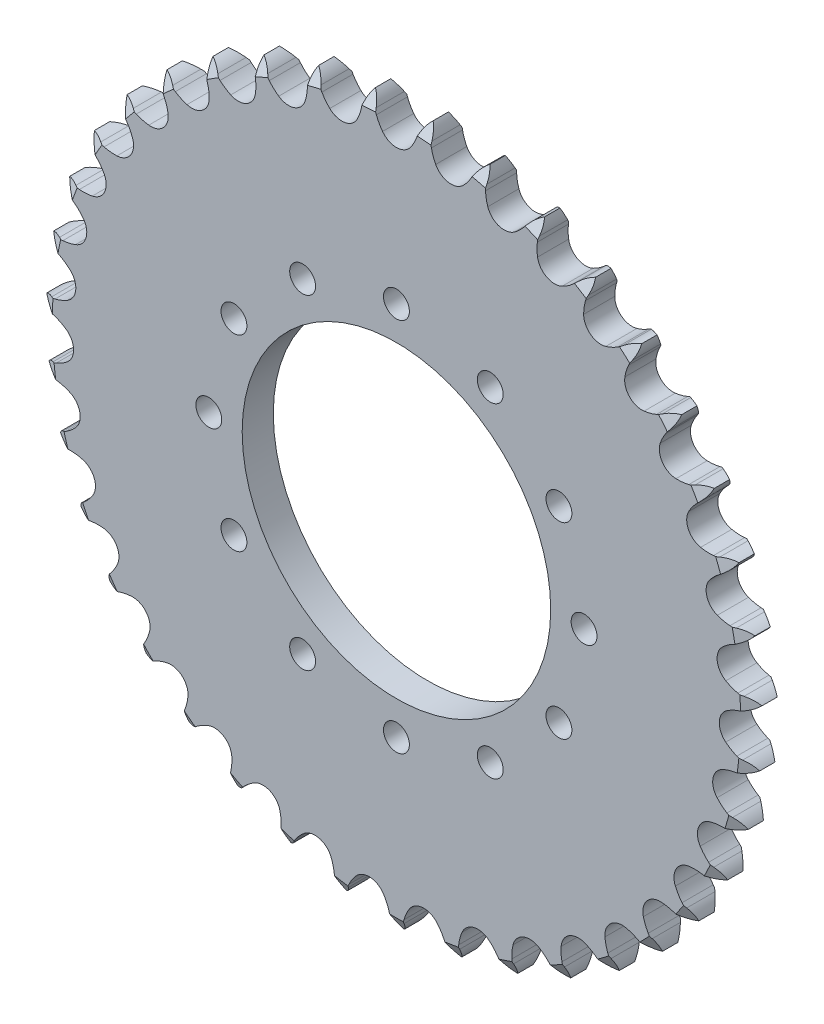
SolidWorks part; units mm, degrees
material "7075-T6 (SN)"
ref_plane "Front Plane" through (0, 0, 0) normal (0, 0, 1) x (1, 0, 0)
ref_plane "Top Plane" through (0, 0, 0) normal (0, 1, 0) x (1, 0, 0)
ref_plane "Right Plane" through (0, 0, 0) normal (1, 0, 0) x (0, 0, -1)
sketch "Work Sketch" plane through (0, 0, 0) normal (0, 0, 1) x (1, 0, 0)
  line L0 (0, 0) -> (0, 160.4542) construction
  line L1 (-112.0919, 78.9148) -> (87.2579, 78.9148) construction
  line L2 (5.102, 120.8822) -> (5.102, 112.9699) construction
  line L3 (-12.8497, 82.6953) -> (16.7256, 82.6953) construction
  line L4 (5.102, 82.6953) -> (-6.0879, 74.4036) construction
  line L5 (5.102, 82.6953) -> (-4.6505, 79.1506) construction
  line L6 (-4.6505, 79.1506) -> (-6.8863, 85.3019)
  line L7 (-11.5114, 78.0206) -> (-7.1525, 78.0206) construction
  line L8 (-11.0765, 124.7602) -> (-11.0765, 110.2345) construction
  line L9 (0, 0) -> (-3.4402, 42.6146) construction
  circle A0 centre (0, 0) radius 78.9148
  circle A1 centre (0, 78.9148) radius 4.0088
  arc A2 (-4.6505, 79.1506) -> (-3.2209, 76.5281) centre (5.0804, 82.7541) ccw
  circle A3 centre (-11.0765, 78.0206) radius 6.4254
  point P23 (-3.2209, 76.5281)
  dimension "D1" = 157.8295
  dimension "D8" = 10.3767
  dimension "D2" = 8.0177
  dimension "D3" = 5.102
  dimension "D4" = 3.7806
  dimension "D5" = 36.538
  dimension "D6" = 16.564
  dimension "D7" = 10.3767
  dimension "D9" = 0.8942
  dimension "D10" = 11.0765
  dimension "D11" = 4.615
sketch "Teeth Sketch" plane through (0, 0, 0) normal (0, 0, 1) x (1, 0, 0)
  line L0 (5.0376, 80.2155) -> (4.6505, 79.1506)
  line L1 (-7.4865, 92.7372) -> (-4.7839, 59.2593) construction
  line L2 (0, 0) -> (-10.9133, 132.3061) construction
  line L3 (7.8951, 79.9848) -> (8.1063, 78.8717)
  line L4 (16093.3137, -199351.4616) -> (-16096.7539, 199394.0762) construction
  line L5 (0, 146.3285) -> (0, 56.9858) construction
  line L6 (17.8398, 78.3686) -> (17.287, 77.3797)
  line L7 (0, -200000) -> (0, 200160.4542) construction
  line L8 (20.6234, 77.6826) -> (20.6533, 76.5499)
  line L9 (-4.6505, 79.1506) -> (-6.8863, 85.3019) construction
  line L10 (44.1616, 67.154) -> (43.8313, 66.0702)
  line L11 (-5.0376, 80.2155) -> (-4.6505, 79.1506)
  line L12 (30.18, 74.4921) -> (29.4757, 73.6046)
  line L13 (32.8175, 73.3684) -> (32.6653, 72.2456)
  line L14 (41.7385, 68.6862) -> (40.901, 67.9232)
  line L15 (52.2161, 61.1014) -> (51.267, 60.4826)
  line L16 (54.362, 59.2003) -> (53.8621, 58.1836)
  line L17 (61.3413, 51.9341) -> (60.3052, 51.4756)
  line L18 (63.1544, 49.7134) -> (62.4979, 48.79)
  line L19 (68.8777, 41.4218) -> (67.7815, 41.1354)
  line L20 (70.3112, 38.939) -> (69.515, 38.1328)
  line L21 (74.6303, 29.8366) -> (73.5023, 29.7298)
  line L22 (75.6469, 27.156) -> (74.7318, 26.488)
  line L23 (78.45, 17.4787) -> (77.3195, 17.5542)
  line L24 (79.0234, 14.6698) -> (78.013, 14.1572)
  line L25 (80.2378, 4.6681) -> (79.1341, 4.9239)
  line L26 (80.3533, 1.8035) -> (79.2737, 1.4597)
  line L27 (79.9476, -8.2634) -> (78.8992, -7.8338)
  line L28 (79.602, -11.1094) -> (78.4813, -11.2756)
  line L29 (77.5867, -20.9809) -> (76.6208, -20.3887)
  line L30 (76.7891, -23.7346) -> (75.6562, -23.7189)
  line L31 (73.2164, -33.155) -> (72.358, -32.4155)
  line L32 (71.9874, -35.7451) -> (70.8717, -35.5478)
  line L33 (66.9499, -44.4704) -> (66.2212, -43.6028)
  line L34 (65.3213, -46.8298) -> (64.2517, -46.4561)
  line L35 (58.9493, -54.634) -> (58.3693, -53.6608)
  line L36 (56.9634, -56.7016) -> (55.9676, -56.1612)
  line L37 (49.422, -63.3827) -> (49.0056, -62.329)
  line L38 (47.1301, -65.1049) -> (46.2339, -64.4118)
  line L39 (38.6147, -70.4897) -> (38.3727, -69.3829)
  line L40 (36.0763, -71.822) -> (35.3028, -70.9941)
  line L41 (26.8073, -75.7712) -> (26.746, -74.6398)
  line L42 (24.088, -76.679) -> (23.4574, -75.7377)
  line L43 (14.3056, -79.0901) -> (14.4266, -77.9636)
  line L44 (11.4759, -79.55) -> (11.0044, -78.5198)
  line L45 (1.4334, -80.3607) -> (1.7335, -79.2682)
  line L46 (-1.4334, -80.3607) -> (-1.7335, -79.2682)
  line L47 (-11.4759, -79.55) -> (-11.0044, -78.5198)
  line L48 (-14.3056, -79.0901) -> (-14.4266, -77.9636)
  line L49 (-24.088, -76.679) -> (-23.4574, -75.7377)
  line L50 (-26.8073, -75.7712) -> (-26.746, -74.6398)
  line L51 (-36.0763, -71.822) -> (-35.3028, -70.9941)
  line L52 (-38.6147, -70.4897) -> (-38.3727, -69.3829)
  line L53 (-47.1301, -65.1049) -> (-46.2339, -64.4118)
  line L54 (-49.422, -63.3827) -> (-49.0056, -62.329)
  line L55 (-56.9634, -56.7016) -> (-55.9676, -56.1612)
  line L56 (-58.9493, -54.634) -> (-58.3693, -53.6608)
  line L57 (-65.3213, -46.8298) -> (-64.2517, -46.4561)
  line L58 (-66.9499, -44.4704) -> (-66.2212, -43.6028)
  line L59 (-71.9874, -35.7451) -> (-70.8717, -35.5478)
  line L60 (-73.2164, -33.155) -> (-72.358, -32.4155)
  line L61 (-76.7891, -23.7346) -> (-75.6562, -23.7189)
  line L62 (-77.5867, -20.9809) -> (-76.6208, -20.3887)
  line L63 (-79.602, -11.1094) -> (-78.4813, -11.2756)
  line L64 (-79.9476, -8.2634) -> (-78.8992, -7.8338)
  line L65 (-80.3533, 1.8035) -> (-79.2737, 1.4597)
  line L66 (-80.2378, 4.6681) -> (-79.1341, 4.9239)
  line L67 (-79.0234, 14.6698) -> (-78.013, 14.1572)
  line L68 (-78.45, 17.4787) -> (-77.3195, 17.5542)
  line L69 (-75.6469, 27.156) -> (-74.7318, 26.488)
  line L70 (-74.6303, 29.8366) -> (-73.5023, 29.7298)
  line L71 (-70.3112, 38.939) -> (-69.515, 38.1328)
  line L72 (-68.8777, 41.4218) -> (-67.7815, 41.1354)
  line L73 (-63.1544, 49.7134) -> (-62.4979, 48.79)
  line L74 (-61.3413, 51.9341) -> (-60.3052, 51.4756)
  line L75 (-54.362, 59.2003) -> (-53.8621, 58.1836)
  line L76 (-52.2161, 61.1014) -> (-51.267, 60.4826)
  line L77 (-44.1616, 67.154) -> (-43.8313, 66.0702)
  line L78 (-41.7385, 68.6862) -> (-40.901, 67.9232)
  line L79 (-32.8175, 73.3684) -> (-32.6653, 72.2456)
  line L80 (-30.18, 74.4921) -> (-29.4757, 73.6046)
  line L81 (-20.6234, 77.6826) -> (-20.6533, 76.5499)
  line L82 (-17.8398, 78.3686) -> (-17.287, 77.3797)
  line L83 (-7.8951, 79.9848) -> (-8.1063, 78.8717)
  arc A0 (-6.8336, 82.8459) -> (-5.0376, 80.2155) centre (-11.0765, 78.0206) cw
  circle A1 centre (-11.0765, 78.0206) radius 6.4254 construction
  arc A2 (-3.2209, 76.5281) -> (-4.6505, 79.1506) centre (5.0804, 82.7541) cw
  arc A3 (-4.6505, 79.1506) -> (-3.2209, 76.5281) centre (5.0804, 82.7541) ccw construction
  circle A4 centre (0, 78.9148) radius 4.0088 construction
  arc A5 (-3.2209, 76.5281) -> (3.2209, 76.5281) centre (0, 78.9148) ccw
  arc A6 (3.2209, 76.5281) -> (4.6505, 79.1506) centre (-5.0804, 82.7541) ccw
  arc A7 (6.8336, 82.8459) -> (5.0376, 80.2155) centre (11.0765, 78.0206) ccw
  arc A8 (6.5443, 82.8692) -> (7.8951, 79.9848) centre (1.5824, 78.787) cw
  arc A9 (9.0967, 76.0537) -> (8.1063, 78.8717) centre (18.2893, 80.8676) cw
  arc A10 (9.0967, 76.0537) -> (15.4552, 75.0204) centre (12.6588, 77.8928) ccw
  arc A11 (15.4552, 75.0204) -> (17.287, 77.3797) centre (8.2601, 82.4975) ccw
  arc A12 (20.0345, 80.6769) -> (17.8398, 78.3686) centre (23.4484, 75.2334) ccw
  arc A13 (19.7528, 80.7463) -> (20.6234, 77.6826) centre (14.2002, 77.5129) cw
  arc A14 (21.1788, 73.6096) -> (20.6533, 76.5499) centre (31.0245, 76.8865) cw
  arc A15 (21.1788, 73.6096) -> (27.2892, 71.5697) centre (24.9898, 74.8535) ccw
  arc A16 (27.2892, 71.5697) -> (29.4757, 73.6046) centre (21.3867, 80.1041) ccw
  arc A17 (32.7165, 76.4184) -> (30.18, 74.4921) centre (35.2131, 70.4978) ccw
  arc A18 (32.4496, 76.5321) -> (32.8175, 73.3684) centre (26.4502, 74.2313) cw
  arc A19 (32.7124, 69.2591) -> (32.6653, 72.2456) centre (42.9562, 70.9142) cw
  arc A20 (32.7124, 69.2591) -> (38.4163, 66.2654) centre (36.6735, 69.8756) ccw
  arc A21 (38.4163, 66.2654) -> (40.901, 67.9232) centre (33.9593, 75.6361) ccw
  arc A22 (44.5512, 70.1807) -> (41.7385, 68.6862) centre (46.0657, 63.9363) ccw
  arc A23 (44.306, 70.3358) -> (44.1616, 67.154) centre (38.0153, 69.0271) cw
  arc A24 (43.3987, 63.1147) -> (43.8313, 66.0702) centre (53.7754, 63.1052) cw
  arc A25 (43.3987, 63.1147) -> (48.5486, 59.2448) centre (47.4074, 63.0878) ccw
  arc A26 (48.5486, 59.2448) -> (51.267, 60.4826) centre (45.6524, 69.2092) ccw
  arc A27 (55.2321, 62.1253) -> (52.2161, 61.1014) centre (55.7253, 55.7189) ccw
  arc A28 (55.0149, 62.3178) -> (54.362, 59.2003) centre (48.5957, 62.0351) cw
  arc A29 (52.961, 55.3358) -> (53.8621, 58.1836) centre (63.2018, 53.6618) cw
  arc A30 (52.961, 55.3358) -> (57.4234, 50.6899) centre (56.9135, 54.6662) ccw
  arc A31 (57.4234, 50.6899) -> (60.3052, 51.4756) centre (56.1632, 60.9898) ccw
  arc A32 (64.4824, 52.461) -> (61.3413, 51.9341) centre (63.9416, 46.0584) ccw
  arc A33 (64.2989, 52.6858) -> (63.1544, 49.7134) centre (57.9175, 53.4365) cw
  arc A34 (61.1517, 46.1237) -> (62.4979, 48.79) centre (70.9913, 42.8287) cw
  arc A35 (61.1517, 46.1237) -> (64.811, 40.8221) centre (64.9456, 44.8287) ccw
  arc A36 (64.811, 40.8221) -> (67.7815, 41.1354) centre (65.2193, 51.1908) ccw
  arc A37 (72.0627, 41.4379) -> (68.8777, 41.4218) centre (70.5018, 35.205) ccw
  arc A38 (71.9177, 41.6892) -> (70.3112, 38.939) centre (65.7393, 43.4539) cw
  arc A39 (67.7585, 35.717) -> (69.515, 38.1328) centre (76.9422, 30.8862) cw
  arc A40 (67.7585, 35.717) -> (70.5201, 29.8971) centre (71.2956, 33.8302) ccw
  arc A41 (70.5201, 29.8971) -> (73.5023, 29.7298) centre (72.5864, 40.0659) ccw
  arc A42 (77.7767, 29.3416) -> (74.6303, 29.8366) centre (75.2361, 23.4398) ccw
  arc A43 (77.6738, 29.6129) -> (75.6469, 27.156) centre (71.8585, 32.3458) cw
  arc A44 (72.6105, 24.3852) -> (74.7318, 26.488) centre (80.9003, 18.1439) cw
  arc A45 (72.6105, 24.3852) -> (74.4027, 18.1977) centre (75.7991, 21.9555) ccw
  arc A46 (74.4027, 18.1977) -> (77.3195, 17.5542) centre (78.0734, 27.9034) ccw
  arc A47 (81.4762, 16.4854) -> (78.45, 17.4787) centre (78.0218, 11.0675) ccw
  arc A48 (81.4182, 16.7697) -> (79.0234, 14.6698) centre (76.1166, 20.4) cw
  arc A49 (75.5818, 12.4219) -> (78.013, 14.1572) centre (82.7631, 4.9316) cw
  arc A50 (75.5818, 12.4219) -> (76.3583, 6.027) centre (78.3394, 9.5121) ccw
  arc A51 (76.3583, 6.027) -> (79.1341, 4.9239) centre (81.5384, 15.0182) ccw
  arc A52 (83.0656, 3.2022) -> (80.2378, 4.6681) centre (78.7868, -1.5914) ccw
  arc A53 (83.0539, 3.4922) -> (80.3533, 1.8035) centre (78.4033, 7.9259) cw
  arc A54 (76.5957, 0.1368) -> (79.2737, 1.4597) centre (82.4825, -8.4084) cw
  arc A55 (76.5957, 0.1368) -> (76.3363, -6.2998) centre (78.8508, -3.1776) ccw
  arc A56 (76.3363, -6.2998) -> (78.8992, -7.8338) centre (82.8916, 1.7441) ccw
  arc A57 (82.5035, -10.1639) -> (79.9476, -8.2634) centre (77.5113, -14.2091) ccw
  arc A58 (82.5385, -9.8758) -> (79.602, -11.1094) centre (78.6594, -4.7535) cw
  arc A59 (75.6257, -12.1517) -> (78.4813, -11.2756) centre (80.0655, -21.5307) cw
  arc A60 (75.6257, -12.1517) -> (74.3372, -18.4634) centre (77.3199, -15.785) ccw
  arc A61 (74.3372, -18.4634) -> (76.6208, -20.3887) centre (82.0979, -11.5753) ccw
  arc A62 (79.8047, -23.2668) -> (77.5867, -20.9809) centre (74.2283, -26.4587) ccw
  arc A63 (79.8855, -22.9881) -> (76.7891, -23.7346) centre (76.8783, -17.3098) cw
  arc A64 (72.6971, -24.1256) -> (75.6562, -23.7189) centre (75.5749, -34.0953) cw
  arc A65 (72.6971, -24.1256) -> (70.4128, -30.1488) centre (73.7866, -27.9836) ccw
  arc A66 (70.4128, -30.1488) -> (72.358, -32.4155) centre (79.178, -24.5948) ccw
  arc A67 (75.039, -35.7671) -> (73.2164, -33.155) centre (69.0227, -38.0232) ccw
  arc A68 (75.1634, -35.5049) -> (71.9874, -35.7451) centre (73.106, -29.4178) cw
  arc A69 (67.8857, -35.4746) -> (70.8717, -35.5478) centre (69.127, -45.7768) cw
  arc A70 (67.8857, -35.4746) -> (64.6648, -41.0534) centre (68.3422, -39.4574) ccw
  arc A71 (64.6648, -41.0534) -> (66.2212, -43.6028) centre (74.2074, -36.9773) ccw
  arc A72 (68.3299, -47.341) -> (66.9499, -44.4704) centre (62.0296, -48.6028) ccw
  arc A73 (68.4947, -47.1022) -> (65.3213, -46.8298) centre (67.4404, -40.7639) cw
  arc A74 (61.3161, -45.9049) -> (64.2517, -46.4561) centre (60.8887, -56.2728) cw
  arc A75 (61.3161, -45.9049) -> (57.2419, -50.8948) centre (61.1278, -49.9093) ccw
  arc A76 (57.2419, -50.8948) -> (58.3693, -53.6608) centre (67.3148, -48.4022) ccw
  arc A77 (59.851, -57.6888) -> (58.9493, -54.634) centre (53.4299, -57.9236) ccw
  arc A78 (60.052, -57.4796) -> (56.9634, -56.7016) centre (60.0281, -51.0542) cw
  arc A79 (53.1584, -55.1462) -> (55.9676, -56.1612) centre (51.0734, -65.3113) cw
  arc A80 (53.1584, -55.1462) -> (48.3366, -59.4179) centre (52.3302, -59.0685) ccw
  arc A81 (48.3366, -59.4179) -> (49.0056, -62.329) centre (58.6789, -58.5735) ccw
  arc A82 (49.822, -66.5425) -> (49.422, -63.3827) centre (43.4464, -65.7443) ccw
  arc A83 (50.054, -66.3682) -> (47.1301, -65.1049) centre (51.0611, -60.0222) cw
  arc A84 (43.6239, -62.9593) -> (46.2339, -64.4118) centre (39.9354, -72.6583) cw
  arc A85 (43.6239, -62.9593) -> (38.1793, -66.4022) centre (42.1772, -66.698) ccw
  arc A86 (38.1793, -66.4022) -> (38.3727, -69.3829) centre (48.5231, -67.2277) ccw
  arc A87 (38.5026, -73.6728) -> (38.6147, -70.4897) centre (32.3376, -71.8622) ccw
  arc A88 (38.7596, -73.538) -> (36.0763, -71.822) centre (40.7716, -67.4357) cw
  arc A89 (32.9596, -69.1417) -> (35.3028, -70.9941) centre (27.763, -78.1234) cw
  arc A90 (32.9596, -69.1417) -> (27.0333, -71.6667) centre (30.932, -72.6) ccw
  arc A91 (27.0333, -71.6667) -> (26.746, -74.6398) centre (37.1107, -74.1408) ccw
  arc A92 (26.1861, -78.8951) -> (26.8073, -75.7712) centre (20.3913, -76.1189) ccw
  arc A93 (26.4613, -78.8032) -> (24.088, -76.679) centre (29.4261, -73.1027) cw
  arc A94 (21.4417, -73.5335) -> (23.4574, -75.7377) centre (14.8716, -81.5653) cw
  arc A95 (21.4417, -73.5335) -> (15.187, -75.0751) centre (18.8855, -76.6216) ccw
  arc A96 (15.187, -75.0751) -> (14.4266, -77.9636) centre (24.7371, -79.1336) ccw
  arc A97 (13.1913, -82.0739) -> (14.3056, -79.0901) centre (7.9169, -78.4042) ccw
  arc A98 (13.4777, -82.0274) -> (11.4759, -79.55) centre (17.3186, -76.8763) cw
  arc A99 (9.3684, -76.0207) -> (11.0044, -78.5198) centre (1.595, -82.8946) cw
  arc A100 (9.3684, -76.0207) -> (2.9475, -76.5391) centre (6.35, -78.6589) ccw
  arc A101 (2.9475, -76.5391) -> (1.7335, -79.2682) centre (11.7228, -82.077) ccw
  arc A102 (-0.1451, -83.1271) -> (1.4334, -80.3607) centre (-4.7625, -78.6589) ccw
  arc A103 (0.1451, -83.1271) -> (-1.4334, -80.3607) centre (4.7625, -78.6589) cw
  arc A104 (-2.9475, -76.5391) -> (-1.7335, -79.2682) centre (-11.7228, -82.077) cw
  arc A105 (-2.9475, -76.5391) -> (-9.3684, -76.0207) centre (-6.35, -78.6589) ccw
  arc A106 (-9.3684, -76.0207) -> (-11.0044, -78.5198) centre (-1.595, -82.8946) ccw
  arc A107 (-13.4777, -82.0274) -> (-11.4759, -79.55) centre (-17.3186, -76.8763) ccw
  arc A108 (-13.1913, -82.0739) -> (-14.3056, -79.0901) centre (-7.9169, -78.4042) cw
  arc A109 (-15.187, -75.0751) -> (-14.4266, -77.9636) centre (-24.7371, -79.1336) cw
  arc A110 (-15.187, -75.0751) -> (-21.4417, -73.5335) centre (-18.8855, -76.6216) ccw
  arc A111 (-21.4417, -73.5335) -> (-23.4574, -75.7377) centre (-14.8716, -81.5653) ccw
  arc A112 (-26.4613, -78.8032) -> (-24.088, -76.679) centre (-29.4261, -73.1027) ccw
  arc A113 (-26.1861, -78.8951) -> (-26.8073, -75.7712) centre (-20.3913, -76.1189) cw
  arc A114 (-27.0333, -71.6667) -> (-26.746, -74.6398) centre (-37.1107, -74.1408) cw
  arc A115 (-27.0333, -71.6667) -> (-32.9596, -69.1417) centre (-30.932, -72.6) ccw
  arc A116 (-32.9596, -69.1417) -> (-35.3028, -70.9941) centre (-27.763, -78.1234) ccw
  arc A117 (-38.7596, -73.538) -> (-36.0763, -71.822) centre (-40.7716, -67.4357) ccw
  arc A118 (-38.5026, -73.6728) -> (-38.6147, -70.4897) centre (-32.3376, -71.8622) cw
  arc A119 (-38.1793, -66.4022) -> (-38.3727, -69.3829) centre (-48.5231, -67.2277) cw
  arc A120 (-38.1793, -66.4022) -> (-43.6239, -62.9593) centre (-42.1772, -66.698) ccw
  arc A121 (-43.6239, -62.9593) -> (-46.2339, -64.4118) centre (-39.9354, -72.6583) ccw
  arc A122 (-50.054, -66.3682) -> (-47.1301, -65.1049) centre (-51.0611, -60.0222) ccw
  arc A123 (-49.822, -66.5425) -> (-49.422, -63.3827) centre (-43.4464, -65.7443) cw
  arc A124 (-48.3366, -59.4179) -> (-49.0056, -62.329) centre (-58.6789, -58.5735) cw
  arc A125 (-48.3366, -59.4179) -> (-53.1584, -55.1462) centre (-52.3302, -59.0685) ccw
  arc A126 (-53.1584, -55.1462) -> (-55.9676, -56.1612) centre (-51.0734, -65.3113) ccw
  arc A127 (-60.052, -57.4796) -> (-56.9634, -56.7016) centre (-60.0281, -51.0542) ccw
  arc A128 (-59.851, -57.6888) -> (-58.9493, -54.634) centre (-53.4299, -57.9236) cw
  arc A129 (-57.2419, -50.8948) -> (-58.3693, -53.6608) centre (-67.3148, -48.4022) cw
  arc A130 (-57.2419, -50.8948) -> (-61.3161, -45.9049) centre (-61.1278, -49.9093) ccw
  arc A131 (-61.3161, -45.9049) -> (-64.2517, -46.4561) centre (-60.8887, -56.2728) ccw
  arc A132 (-68.4947, -47.1022) -> (-65.3213, -46.8298) centre (-67.4404, -40.7639) ccw
  arc A133 (-68.3299, -47.341) -> (-66.9499, -44.4704) centre (-62.0296, -48.6028) cw
  arc A134 (-64.6648, -41.0534) -> (-66.2212, -43.6028) centre (-74.2074, -36.9773) cw
  arc A135 (-64.6648, -41.0534) -> (-67.8857, -35.4746) centre (-68.3422, -39.4574) ccw
  arc A136 (-67.8857, -35.4746) -> (-70.8717, -35.5478) centre (-69.127, -45.7768) ccw
  arc A137 (-75.1634, -35.5049) -> (-71.9874, -35.7451) centre (-73.106, -29.4178) ccw
  arc A138 (-75.039, -35.7671) -> (-73.2164, -33.155) centre (-69.0227, -38.0232) cw
  arc A139 (-70.4128, -30.1488) -> (-72.358, -32.4155) centre (-79.178, -24.5948) cw
  arc A140 (-70.4128, -30.1488) -> (-72.6971, -24.1256) centre (-73.7866, -27.9836) ccw
  arc A141 (-72.6971, -24.1256) -> (-75.6562, -23.7189) centre (-75.5749, -34.0953) ccw
  arc A142 (-79.8855, -22.9881) -> (-76.7891, -23.7346) centre (-76.8783, -17.3098) ccw
  arc A143 (-79.8047, -23.2668) -> (-77.5867, -20.9809) centre (-74.2283, -26.4587) cw
  arc A144 (-74.3372, -18.4634) -> (-76.6208, -20.3887) centre (-82.0979, -11.5753) cw
  arc A145 (-74.3372, -18.4634) -> (-75.6257, -12.1517) centre (-77.3199, -15.785) ccw
  arc A146 (-75.6257, -12.1517) -> (-78.4813, -11.2756) centre (-80.0655, -21.5307) ccw
  arc A147 (-82.5385, -9.8758) -> (-79.602, -11.1094) centre (-78.6594, -4.7535) ccw
  arc A148 (-82.5035, -10.1639) -> (-79.9476, -8.2634) centre (-77.5113, -14.2091) cw
  arc A149 (-76.3363, -6.2998) -> (-78.8992, -7.8338) centre (-82.8916, 1.7441) cw
  arc A150 (-76.3363, -6.2998) -> (-76.5957, 0.1368) centre (-78.8508, -3.1776) ccw
  arc A151 (-76.5957, 0.1368) -> (-79.2737, 1.4597) centre (-82.4825, -8.4084) ccw
  arc A152 (-83.0539, 3.4922) -> (-80.3533, 1.8035) centre (-78.4033, 7.9259) ccw
  arc A153 (-83.0656, 3.2022) -> (-80.2378, 4.6681) centre (-78.7868, -1.5914) cw
  arc A154 (-76.3583, 6.027) -> (-79.1341, 4.9239) centre (-81.5384, 15.0182) cw
  arc A155 (-76.3583, 6.027) -> (-75.5818, 12.4219) centre (-78.3394, 9.5121) ccw
  arc A156 (-75.5818, 12.4219) -> (-78.013, 14.1572) centre (-82.7631, 4.9316) ccw
  arc A157 (-81.4182, 16.7697) -> (-79.0234, 14.6698) centre (-76.1166, 20.4) ccw
  arc A158 (-81.4762, 16.4854) -> (-78.45, 17.4787) centre (-78.0218, 11.0675) cw
  arc A159 (-74.4027, 18.1977) -> (-77.3195, 17.5542) centre (-78.0734, 27.9034) cw
  arc A160 (-74.4027, 18.1977) -> (-72.6105, 24.3852) centre (-75.7991, 21.9555) ccw
  arc A161 (-72.6105, 24.3852) -> (-74.7318, 26.488) centre (-80.9003, 18.1439) ccw
  arc A162 (-77.6738, 29.6129) -> (-75.6469, 27.156) centre (-71.8585, 32.3458) ccw
  arc A163 (-77.7767, 29.3416) -> (-74.6303, 29.8366) centre (-75.2361, 23.4398) cw
  arc A164 (-70.5201, 29.8971) -> (-73.5023, 29.7298) centre (-72.5864, 40.0659) cw
  arc A165 (-70.5201, 29.8971) -> (-67.7585, 35.717) centre (-71.2956, 33.8302) ccw
  arc A166 (-67.7585, 35.717) -> (-69.515, 38.1328) centre (-76.9422, 30.8862) ccw
  arc A167 (-71.9177, 41.6892) -> (-70.3112, 38.939) centre (-65.7393, 43.4539) ccw
  arc A168 (-72.0627, 41.4379) -> (-68.8777, 41.4218) centre (-70.5018, 35.205) cw
  arc A169 (-64.811, 40.8221) -> (-67.7815, 41.1354) centre (-65.2193, 51.1908) cw
  arc A170 (-64.811, 40.8221) -> (-61.1517, 46.1237) centre (-64.9456, 44.8287) ccw
  arc A171 (-61.1517, 46.1237) -> (-62.4979, 48.79) centre (-70.9913, 42.8287) ccw
  arc A172 (-64.2989, 52.6858) -> (-63.1544, 49.7134) centre (-57.9175, 53.4365) ccw
  arc A173 (-64.4824, 52.461) -> (-61.3413, 51.9341) centre (-63.9416, 46.0584) cw
  arc A174 (-57.4234, 50.6899) -> (-60.3052, 51.4756) centre (-56.1632, 60.9898) cw
  arc A175 (-57.4234, 50.6899) -> (-52.961, 55.3358) centre (-56.9135, 54.6662) ccw
  arc A176 (-52.961, 55.3358) -> (-53.8621, 58.1836) centre (-63.2018, 53.6618) ccw
  arc A177 (-55.0149, 62.3178) -> (-54.362, 59.2003) centre (-48.5957, 62.0351) ccw
  arc A178 (-55.2321, 62.1253) -> (-52.2161, 61.1014) centre (-55.7253, 55.7189) cw
  arc A179 (-48.5486, 59.2448) -> (-51.267, 60.4826) centre (-45.6524, 69.2092) cw
  arc A180 (-48.5486, 59.2448) -> (-43.3987, 63.1147) centre (-47.4074, 63.0878) ccw
  arc A181 (-43.3987, 63.1147) -> (-43.8313, 66.0702) centre (-53.7754, 63.1052) ccw
  arc A182 (-44.306, 70.3358) -> (-44.1616, 67.154) centre (-38.0153, 69.0271) ccw
  arc A183 (-44.5512, 70.1807) -> (-41.7385, 68.6862) centre (-46.0657, 63.9363) cw
  arc A184 (-38.4163, 66.2654) -> (-40.901, 67.9232) centre (-33.9593, 75.6361) cw
  arc A185 (-38.4163, 66.2654) -> (-32.7124, 69.2591) centre (-36.6735, 69.8756) ccw
  arc A186 (-32.7124, 69.2591) -> (-32.6653, 72.2456) centre (-42.9562, 70.9142) ccw
  arc A187 (-32.4496, 76.5321) -> (-32.8175, 73.3684) centre (-26.4502, 74.2313) ccw
  arc A188 (-32.7165, 76.4184) -> (-30.18, 74.4921) centre (-35.2131, 70.4978) cw
  arc A189 (-27.2892, 71.5697) -> (-29.4757, 73.6046) centre (-21.3867, 80.1041) cw
  arc A190 (-27.2892, 71.5697) -> (-21.1788, 73.6096) centre (-24.9898, 74.8535) ccw
  arc A191 (-21.1788, 73.6096) -> (-20.6533, 76.5499) centre (-31.0245, 76.8865) ccw
  arc A192 (-19.7528, 80.7463) -> (-20.6234, 77.6826) centre (-14.2002, 77.5129) ccw
  arc A193 (-20.0345, 80.6769) -> (-17.8398, 78.3686) centre (-23.4484, 75.2334) cw
  arc A194 (-15.4552, 75.0204) -> (-17.287, 77.3797) centre (-8.2601, 82.4975) cw
  arc A195 (-15.4552, 75.0204) -> (-9.0967, 76.0537) centre (-12.6588, 77.8928) ccw
  arc A196 (-9.0967, 76.0537) -> (-8.1063, 78.8717) centre (-18.2893, 80.8676) ccw
  arc A197 (-6.5443, 82.8692) -> (-7.8951, 79.9848) centre (-1.5824, 78.787) ccw
  point P77 (0, 0)
  dimension "D1" = 4.615
  dimension "D2" = 4.715
  dimension "D3" = 39
extrude "Extrusion" add sketch "Teeth Sketch" along normal blind 7.2136
sketch "Sketch1" plane through (0, 0, 0) normal (0, 0, -1) x (-1, 0, 0)
  circle A0 centre (0, 0) radius 78.9443
  circle A1 centre (0, 0) radius 35.7643
  dimension "D1" = 43.18
extrude "Cut-Extrude" cut sketch "Sketch1" against normal through all both and the other way through all contours A1
ref_axis "Axis1" [suppressed] through (0, 0, 7.2136) along (0, 0, -1)
ref_plane "Sprocket Center Plane" through (0, 0, 3.6068) normal (0, 0, 1) x (1, 0, 0)
sketch "Pitch Circle" plane through (0, 0, 3.6068) normal (0, 0, -1) x (-1, 0, 0)
  circle A0 centre (0, 0) radius 82.9531 construction
  dimension "D1" = 165.9063
sketch "Chain Pitch Circle" plane through (0, 0, 0) normal (0, 0, -1) x (-1, 0, 0)
  circle A0 centre (0, 0) radius 82.9531 construction
  dimension "D1" = 165.9063
ref_plane "Center Plane" through (0, 0, 3.6068) normal (0, 0, 1) x (1, 0, 0)
hole_wizard "Ø6.0mm Dowel Hole1" positions "Sketch7" profile "Sketch8" hole size "Ø6.0" standard "ANSI Metric" end condition through all
sketch "Sketch7" plane through (0, 0, 7.2136) normal (0, 0, 1) x (1, 0, 0)
  point P0 (-43.5, 0)
  dimension "D1" = 43.5
sketch "Sketch8" plane through (-43.5, 0, 7.2136) normal (1, 0, 0) x (0, -1, 0)
  line L0 (0, 0) -> (0, 7.2136)
  line L1 (0, 7.2136) -> (3, 7.2136)
  line L2 (3, 7.2136) -> (3, 0)
  line L5 (3, 0) -> (0, 0)
  line L11 (0, -6.35) -> (0, 107.95) construction
  dimension "Thru Hole Dia." = 6
  dimension "Thru Hole Depth" = 7.2136
pattern_circular "CirPattern1" count 12 over 360 about axis through (0, 0, 0) along (0, 0, 1) of "Ø6.0mm Dowel Hole1"
sketch "Sketch5" plane through (0, 0, 0) normal (1, 0, 0) x (0, 0, -1)
  line L0 (-1.8288, -82.9722) -> (-5.3848, -82.9722)
  line L3 (-5.3848, -79.7786) -> (-7.2136, -79.7786)
  line L5 (-7.2136, -79.7786) -> (-7.2136, -82.9722)
  line L6 (-7.2136, -82.9722) -> (-5.3848, -82.9722)
  line L7 (-7.2136, -82.9722) -> (0, -82.9722) construction
  line L8 (-7.2136, -82.9722) -> (0, -82.9722)
  line L9 (-5.3848, -82.9722) -> (-7.2136, -79.7786)
  line L10 (-5.3848, -79.7786) -> (-5.3848, -82.9722)
  point P5 (-3.6068, -82.9722)
  dimension "D1" = 3.556
  dimension "D2" = 3.1936
  dimension "D3" = 1.8288
revolve "Cut-Revolve1" cut sketch "Sketch5" angle 360 about axis through (0, 0, 7.2136) along (0, 0, -1)
mirror "Mirror1" about plane through (0, 0, 3.6068) normal (0, 0, 1) of "Cut-Revolve1"
equation "\"P\"= 0.500'//Chain Pitch"
equation "\"N\"= 39'//Number of Teeth"
equation "\"Dr\"= 5 / 16'//Roller Diameter"
equation "\"Ds\"= 1.0005 * \"Dr\" + 0.003'Seating Curve DIameter"
equation "\"R\"= \"Ds\" / 2"
equation "\"A\"= 35 + 60 / \"N\""
equation "\"B\"= 18 - 56 / \"N\""
equation "\"ac\"= 0.8 * \"Dr\""
equation "\"M\"= 0.8 * \"Dr\" * cos ( 35 + 60 / \"N\" )"
equation "\"T\"= 0.8 * \"Dr\" * sin ( 35 + 60 / \"N\" )"
equation "\"E\"= 1.3025 * \"Dr\" + 0.0015"
equation "\"Chordal Length of Arc xy\"= ( 2.605 * \"Dr\" + 0.003 ) * sin ( 9 - 28 / \"N\" )"
equation "\"yz\"= \"Dr\" * ( 1.4 * sin ( 17 - 64 / \"N\" ) - 0.8 * sin ( 18 - 56 / \"N\" ) )"
equation "\"ab\"= 1.4 * \"Dr\""
equation "\"W\"= 1.4 * \"Dr\" * cos ( 180 / \"N\" )"
equation "\"V\"= 1.4 * \"Dr\" * sin ( 180 / \"N\" )"
equation "\"F\"= \"Dr\" * ( 0.8 * cos ( 18 - 56 / \"N\" ) + 1.4 * cos ( 17 - 64 / \"N\" ) - 1.3025 )"
equation "\"H\"= sqr ( \"F\" ^ 2 - ( 1.4 * \"Dr\" - \"P\" / 2 ) ^ 2 )"
equation "\"S\"= \"P\" / 2 * cos ( 180 / \"N\" ) + \"H\" * sin ( 180 / \"N\" )"
equation "\"PD\"= \"P\" / ( sin ( 180 / \"N\" ) )"
equation "\"D1@Work Sketch\" = \"PD\""
equation "\"D3@Work Sketch\" = \"M\""
equation "\"D4@Work Sketch\" = \"T\""
equation "\"D5@Work Sketch\" = \"A\""
equation "\"D6@Work Sketch\" = \"B\""
equation "\"D7@Work Sketch\" = \"E\""
equation "\"D8@Work Sketch\" = \"E\""
equation "\"D9@Work Sketch\" = \"V\""
equation "\"D10@Work Sketch\" = \"W\""
equation "\"D2@Work Sketch\" = \"R\" * 2"
equation "\"D11@Work Sketch\" = 180 / \"N\""
equation "\"D2@Teeth Sketch\" = 180 / \"N\" + 0.1"
equation "\"D3@Teeth Sketch\" = \"N\""
equation "\"Edge Thickness\"=1.7"
equation "\"D1@Sketch1\"=\"Edge Thickness\""
equation "\"ST\"= 0.284'//Sprocket Thickness"
